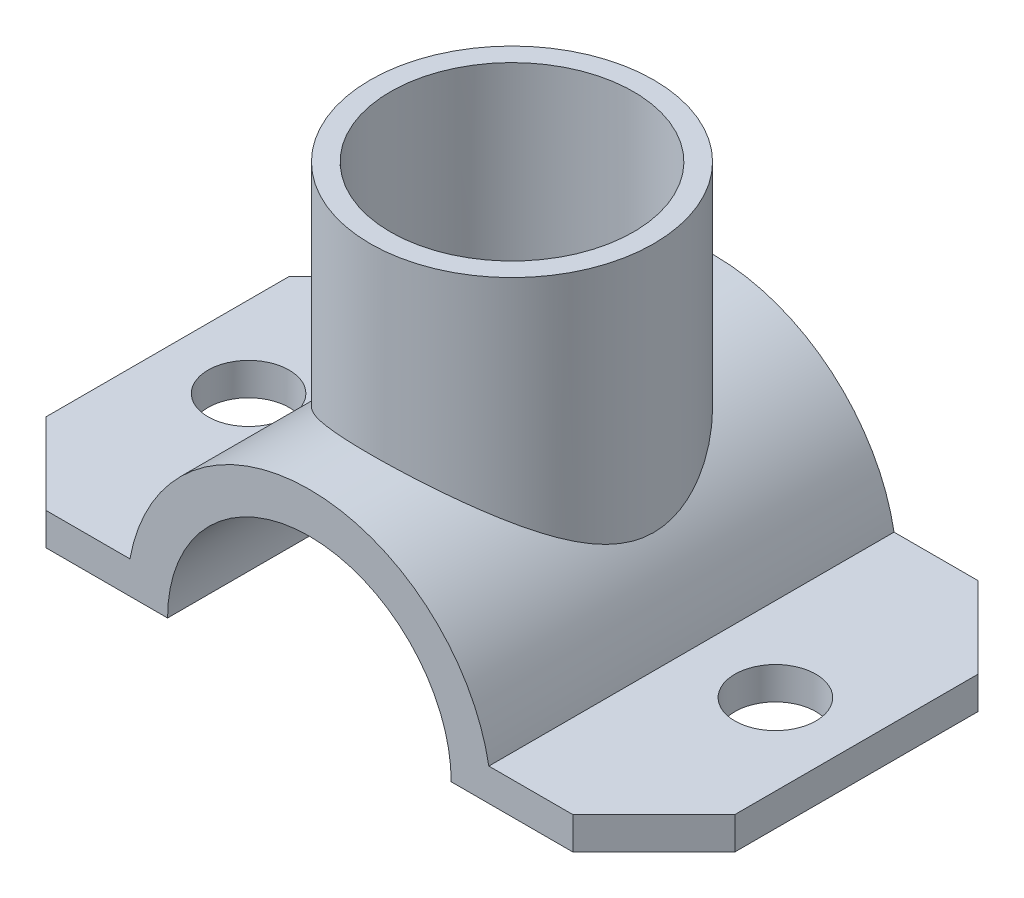
SolidWorks part; units mm, degrees
ref_plane "Front Plane" through (0, 0, 0) normal (0, 0, 1) x (1, 0, 0)
ref_plane "Top Plane" through (0, 0, 0) normal (0, 1, 0) x (1, 0, 0)
ref_plane "Right Plane" through (0, 0, 0) normal (1, 0, 0) x (0, 0, -1)
sketch "Sketch1" plane through (0, 0, 0) normal (0, 0, 1) x (1, 0, 0)
  line L0 (-73.4218, 0) -> (80.5364, 0) construction
  line L1 (-17.5, 0) -> (-42.5, 0)
  line L2 (17.5, 0) -> (42.5, 0)
  line L3 (-22.1416, 4) -> (-42.5, 4)
  line L4 (22.1416, 4) -> (42.5, 4)
  line L5 (-21.1246, 4) -> (-42.5, 4) construction
  line L6 (21.1246, 4) -> (42.5, 4) construction
  line L7 (-42.5, 4) -> (-42.5, 0)
  line L8 (42.5, 4) -> (42.5, 0)
  arc A0 (22.1416, 4) -> (-22.1416, 4) centre (0, 0) ccw
  arc A1 (17.5, 0) -> (-17.5, 0) centre (0, 0) ccw
  arc A3 (21.1246, 4) -> (-21.1246, 4) centre (0, 0) ccw construction
  dimension "D1" = 45
  dimension "D2" = 35
  dimension "D3" = 25
  dimension "D4" = 25
  dimension "D5" = 4
extrude "Boss-Extrude1" add sketch "Sketch1" along normal mid plane 50
chamfer "Chamfer1" distance 10 angle 45 4 edges at (-42.5, 2, -25) (-42.5, 2, 25) (42.5, 2, -25) (42.5, 2, 25)
sketch "Sketch2" plane through (0, 4, 0) normal (0, 1, 0) x (1, 0, 0)
  line L0 (-42.5, -15) -> (-42.5, 15) construction
  line L1 (42.5, -15) -> (42.5, 15) construction
  circle A0 centre (32.5, 0) radius 5
  circle A1 centre (-32.5, 0) radius 5
  dimension "D3" = 10
  dimension "D4" = 10
  dimension "D1" = 10
  dimension "D2" = 10
extrude "Cut-Extrude1" cut sketch "Sketch2" against normal blind 50
ref_plane "Plane1" through (0, 45, 0) normal (0, 1, 0) x (1, 0, 0)
sketch "Sketch3" plane through (0, 45, 0) normal (0, 1, 0) x (1, 0, 0)
  circle A0 centre (0, 0) radius 15
  circle A1 centre (0, 0) radius 17.5
  dimension "D1" = 30
  dimension "D2" = 35
extrude "Boss-Extrude2" add sketch "Sketch3" against normal up to surface (22.5 mm away)
sketch "Sketch4" plane through (0, 45, 0) normal (0, 1, 0) x (1, 0, 0)
  circle A0 centre (0, 0) radius 7.5
  dimension "D1" = 15
extrude "Cut-Extrude2" cut sketch "Sketch4" against normal blind 50
